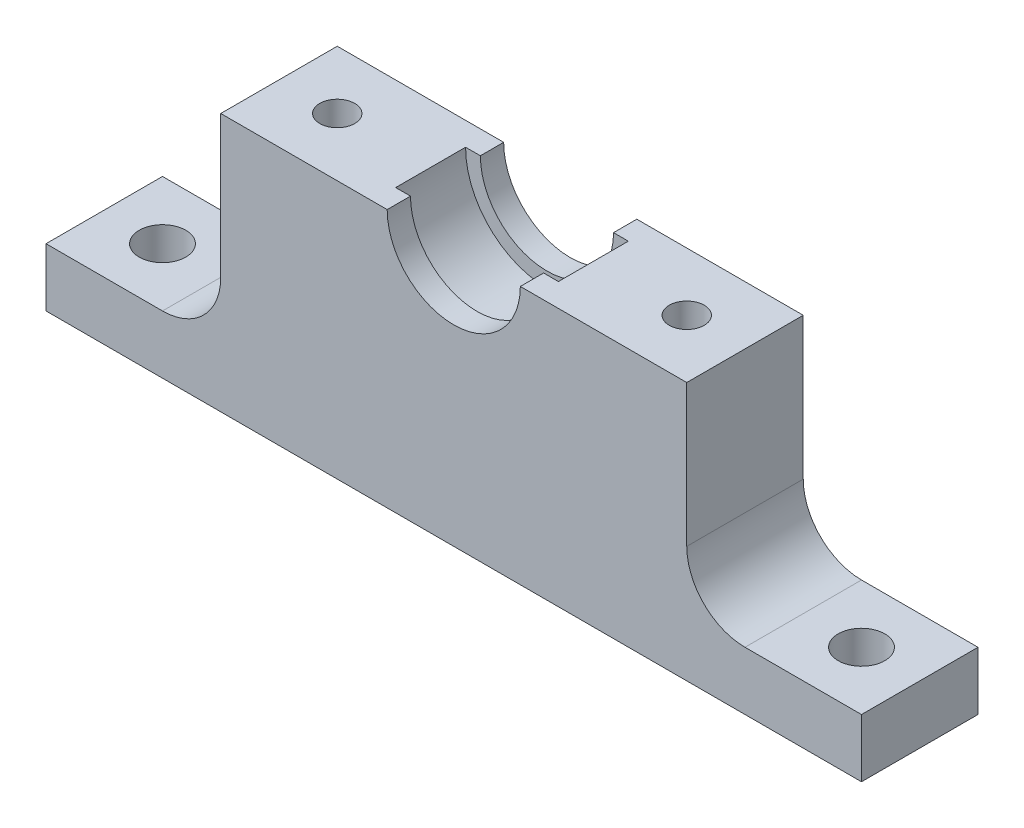
SolidWorks part; units mm, degrees
ref_plane "Front Plane" through (0, 0, 0) normal (0, 0, 1) x (1, 0, 0)
ref_plane "Top Plane" through (0, 0, 0) normal (0, 1, 0) x (1, 0, 0)
ref_plane "Right Plane" through (0, 0, 0) normal (1, 0, 0) x (0, 0, -1)
sketch "Sketch1" plane through (0, 0, 0) normal (0, 1, 0) x (1, 0, 0)
  line L1 (20, -5) -> (-20, -5)
  line L2 (20, -5) -> (20, 5)
  line L3 (20, 5) -> (-20, 5)
  line L4 (-20, -5) -> (-20, 5)
  line L5 (20, -5) -> (-20, 5) construction
  line L6 (20, 5) -> (-20, -5) construction
  point P0 (0, 0)
  dimension "D1" = 40
  dimension "D2" = 10
extrude "Boss-Extrude1" add sketch "Sketch1" along normal blind 22.1798
ref_plane "Plane2" through (0, 0, 0) normal (0, 0, -1) x (-1, 0, 0)
sketch "Sketch2" plane through (0, 0, 0) normal (0, 0, -1) x (-1, 0, 0)
  line L0 (-20, 22.1798) -> (20, 22.1798) construction
  line L1 (-6.985, 22.1798) -> (6.985, 22.1798)
  arc A0 (-6.985, 22.1798) -> (6.985, 22.1798) centre (0, 22.1798) ccw
  dimension "D1" = 13.97
extrude "Cut-Extrude1" cut sketch "Sketch2" against normal mid plane 6
sketch "Sketch3" plane through (0, 0, 0) normal (0, 0, -1) x (-1, 0, 0)
  line L0 (-20, 22.1798) -> (20, 22.1798) construction
  line L1 (-5.715, 22.1798) -> (5.715, 22.1798)
  arc A0 (-5.715, 22.1798) -> (5.715, 22.1798) centre (0, 22.1798) ccw
  dimension "D1" = 11.43
extrude "Cut-Extrude2" cut sketch "Sketch3" against normal mid plane 10
sketch "Sketch4" plane through (0, 22.1798, 0) normal (0, 1, 0) x (1, 0, 0)
  line L0 (0, -5) -> (0, 5) construction
  line L1 (5.715, 5) -> (-5.715, 5) construction
  line L2 (20, -5) -> (20, 5) construction
  circle A0 centre (15, 0) radius 1.5
  circle A1 centre (-15, 0) radius 1.5
  point P6 (0, 0)
  point P12 (20, 0)
  dimension "D1" = 3
  dimension "D2" = 5
extrude "Cut-Extrude3" cut sketch "Sketch4" against normal blind 7
sketch "Sketch5" plane through (0, 0, 0) normal (0, -1, 0) x (1, 0, 0)
  line L0 (-20, -5) -> (-20, 5) construction
  line L1 (-35, 5) -> (-20, 5)
  line L2 (-35, 5) -> (-35, -5)
  line L3 (-35, -5) -> (-20, -5)
  line L4 (-20, 5) -> (-20, -5)
  line L5 (-35, 5) -> (-20, -5) construction
  line L6 (-35, -5) -> (-20, 5) construction
  line L7 (20, -5) -> (-20, -5) construction
  line L8 (-20, 5) -> (20, 5) construction
  line L9 (0, -5) -> (0, 5) construction
  line L10 (35, -5) -> (20, -5)
  line L11 (20, 5) -> (20, -5)
  line L12 (35, 5) -> (20, 5)
  line L13 (35, 5) -> (35, -5)
  circle A0 centre (-30, 0) radius 2
  circle A1 centre (30, 0) radius 2
  point P0 (-27.5, 0)
  point P15 (0, 0)
  dimension "D1" = 4
  dimension "D2" = 15
  dimension "D3" = 5
extrude "Boss-Extrude2" add sketch "Sketch5" against normal blind 5
fillet "Fillet1" radius 5 2 edges at (-20, 5, 0) (20, 5, 0)
